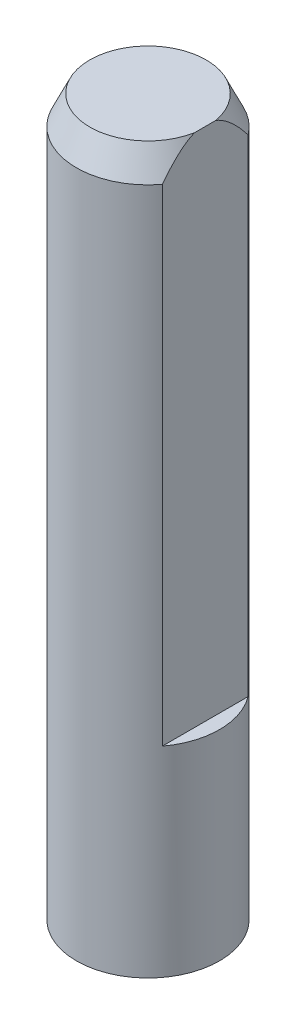
SolidWorks part; units mm, degrees
ref_plane "前视基准面" through (0, 0, 0) normal (0, 0, 1) x (1, 0, 0)
ref_plane "上视基准面" through (0, 0, 0) normal (0, 1, 0) x (1, 0, 0)
ref_plane "右视基准面" through (0, 0, 0) normal (1, 0, 0) x (0, 0, -1)
sketch "草图1" plane through (0, 0, 0) normal (0, 1, 0) x (1, 0, 0)
  circle A0 centre (0, 0) radius 2.5
  dimension "D1" = 5
extrude "凸台-拉伸1" add sketch "草图1" along normal blind 25
sketch "草图2" plane through (0, 25, 0) normal (0, 1, 0) x (1, 0, 0)
  line L0 (0, 2.5) -> (0, -2.5) construction
  line L1 (2, 2.599) -> (2, -2.3616)
  line L2 (2, 2.599) -> (3.8742, -0.7483)
  line L3 (3.8742, -0.7483) -> (3.7776, -1.7581)
  line L4 (3.7776, -1.7581) -> (2.9371, -2.0128)
  line L5 (2.9371, -2.0128) -> (2, -2.3616)
  line L6 (0, 0) -> (-2.5, 0) construction
  circle A0 centre (0, 0) radius 2.5 construction
  dimension "D1" = 4.5
extrude "切除-拉伸1" cut sketch "草图2" against normal blind 18
chamfer "倒角1" distance 1 angle 25 1 edges at (-2.5, 25, 0)
